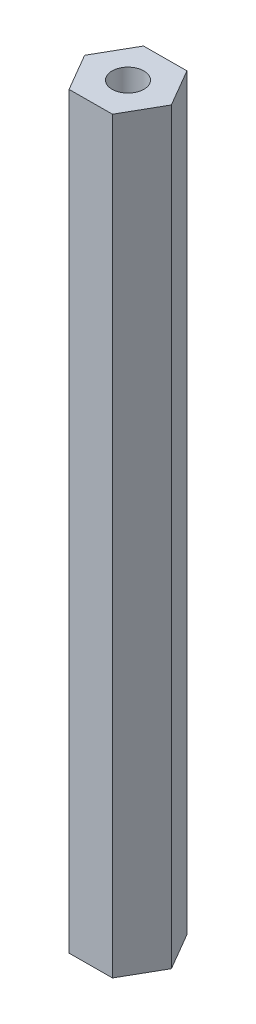
SolidWorks part; units mm, degrees
ref_plane "Front" through (0, 0, 0) normal (0, 0, 1) x (1, 0, 0)
ref_plane "Top" through (0, 0, 0) normal (0, 1, 0) x (1, 0, 0)
ref_plane "Right" through (0, 0, 0) normal (1, 0, 0) x (0, 0, -1)
sketch "Sketch1" plane through (0, 0, 0) normal (0, 1, 0) x (1, 0, 0)
  line L1 (-1.8473, 3.1668) -> (-3.6661, -0.0164)
  line L2 (-3.6661, -0.0164) -> (-1.8189, -3.1832)
  line L3 (-1.8189, -3.1832) -> (1.8473, -3.1668)
  line L4 (1.8473, -3.1668) -> (3.6661, 0.0164)
  line L5 (3.6661, 0.0164) -> (1.8189, 3.1832)
  line L6 (1.8189, 3.1832) -> (-1.8473, 3.1668)
  circle A0 centre (0, 0) radius 3.175 construction
  dimension "D1" = 6.35
extrude "Boss-Extrude1" add sketch "Sketch1" along normal blind 63.5
sketch "Sketch2" plane through (0, 63.5, 0) normal (0, 1, 0) x (1, 0, 0)
  circle A0 centre (0, 0) radius 1.3525
  dimension "D1" = 2.7051
extrude "Cut-Extrude1" cut sketch "Sketch2" against normal through all
